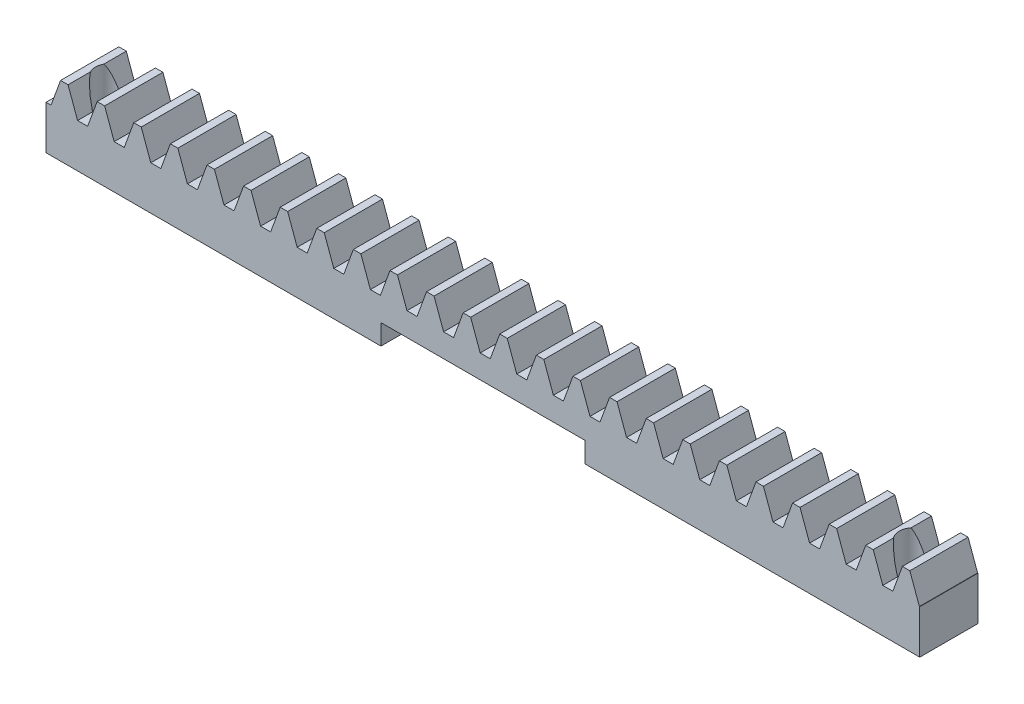
SolidWorks part; units mm, degrees
extrude "Blank" add sketch "BlankSke" against normal blind 10
sketch "BlankSke" plane through (0, 0, 0) normal (0, 0, 1) x (1, 0, 0)
  line L1 (0, 0) -> (150, 0)
  line L2 (0, 0) -> (0, 12)
  line L3 (0, 12) -> (150, 12)
  line L4 (150, 0) -> (150, 12)
  dimension "Length" = 150
  dimension "Blank_height" = 12
ref_plane "Plane1" through (0, 0, 0) normal (0, 0, 1) x (1, 0, 0)
ref_plane "Plane2" through (0, 0, 0) normal (0, 1, 0) x (1, 0, 0)
ref_plane "Plane3" through (0, 0, 0) normal (1, 0, 0) x (0, 0, -1)
other "Configuration Table"
sketch "HoldingSke" plane through (0, 0, 0) normal (0, 1, 0) x (1, 0, 0)
  line L0 (0, 0) -> (0.0696, 0.4951)
  line L1 (-15, 0) -> (100, 0) construction
  line L2 (0, 0) -> (-2.1039, 2.3779)
  line L3 (0, 0) -> (-11.863, 4.5341)
  line L4 (0, 0) -> (7.8269, 3.6497)
  line L5 (0, 0) -> (-23.7986, -8.8762)
  line L6 (0, 0) -> (-10.5278, -7.1032)
  line L9 (-71.009, 38.7566) -> (69.9449, 90.0596)
  line L10 (-76.2, 4.3779) -> (-66.2, 4.3779)
  line L11 (0, 0) -> (-10, 0)
  line L12 (-76.2, 101.6) -> (-76.133, 101.6)
  line L13 (24.9733, 27.94) -> (52.9518, 28.4284)
  line L14 (24.9733, 27.94) -> (24.9743, 27.94)
  line L15 (24.9733, 27.94) -> (100.4006, 29.5858)
  circle A0 centre (0, 0) radius 19.05
  circle A1 centre (0, 0) radius 5
  circle A2 centre (0, 0) radius 12.7
  dimension "MPH" = 10
  dimension "Diameter" = 38.1
  dimension "Num_teeth" = 25
  dimension "Pitch" = 0.5
  dimension "Show_teeth" = 998
  dimension "Thickness" = 12.7
  dimension "Ap" = 20
  dimension "Pitch_height" = 10
  dimension "Width" = 10
  dimension "Backlash" = 0.067
  dimension "Addendum_fac" = 1
  dimension "Dedendum_fac" = 1.25
  dimension "Clearance_fac" = 0.25
  dimension "Dedendum_add" = 0.001
  dimension "Length" = 150
  dimension "Module" = 2
sketch "TooCutSkeIll" plane through (0, 0, 0) normal (0, 0, 1) x (1, 0, 0)
  line L0 (-2.4806, 11.9474) -> (-0.9819, 7.8296)
  line L1 (-0.5111, 7.5) -> (0.5111, 7.5)
  line L2 (0.9819, 7.8296) -> (2.4806, 11.9474)
  line L3 (150, 12) -> (0, 12) construction
  line L4 (0, 0) -> (0, 64.897) construction
  line L5 (-13.208, 10) -> (12.954, 10) construction
  line L6 (0, 0) -> (150, 0) construction
  line L7 (1.7718, 10) -> (1.7718, 48.7463) construction
  line L8 (-1.7718, 10) -> (-1.7718, 48.7463) construction
  line L9 (2.5558, 12) -> (2.5558, 12.0254)
  line L10 (-2.5558, 12) -> (-2.5558, 12.0254)
  line L11 (-2.5558, 12.0254) -> (2.5558, 12.0254)
  arc A0 (0.5111, 7.5) -> (0.9819, 7.8296) centre (0.5111, 8.001) ccw
  arc A1 (-0.9819, 7.8296) -> (-0.5111, 7.5) centre (-0.5111, 8.001) ccw
  arc A2 (2.5558, 12) -> (2.4806, 11.9474) centre (2.5558, 11.92) ccw
  arc A3 (-2.4806, 11.9474) -> (-2.5558, 12) centre (-2.5558, 11.92) ccw
  dimension "Pitch_height" = 10
  dimension "Addendum_plus" = 2.0254
  dimension "Pressure_angle" = 20
  dimension "Gap_width" = 3.5436
  dimension "Dedendum" = 2.5
extrude "ToothCutIll" [suppressed] cut sketch "TooCutSkeIll" against normal through all
sketch "TooCutSkeSim" plane through (0, 0, 0) normal (0, 0, 1) x (1, 0, 0)
  line L0 (0.8619, 7.5) -> (-0.8619, 7.5)
  line L1 (2.509, 12.0254) -> (0.8619, 7.5)
  line L2 (0, 17.4625) -> (0, 53.467) construction
  line L3 (2.509, 12.0254) -> (-2.509, 12.0254)
  line L6 (-2.509, 12.0254) -> (-0.8619, 7.5)
  line L9 (-1.7718, 10) -> (1.7718, 10) construction
  line L10 (0, 0) -> (150, 0) construction
  line L11 (1.7718, 10) -> (1.7718, 53.467) construction
  line L12 (-1.7718, 10) -> (-1.7718, 53.467) construction
  dimension "Pitch_height" = 10
  dimension "Addendum_plus" = 2.0254
  dimension "Pressure_angle" = 20
  dimension "Gap_width" = 3.5436
  dimension "Dedendum" = 2.5
extrude "ToothCutSim" cut sketch "TooCutSkeSim" against normal through all
pattern_linear "TeethCuts" count 25 spacing 6.2832 along (1, 0, 0) of "ToothCutIll", "ToothCutSim"
sketch "Sketch1" plane through (0, 0, 0) normal (0, -1, 0) x (1, 0, 0)
  line L0 (75, 0) -> (75, -10) construction
  line L1 (0, 0) -> (150, 0) construction
  line L2 (0, -10) -> (150, -10) construction
  line L3 (57.5, -10) -> (57.5, 0)
  line L4 (92.5, -10) -> (57.5, -10)
  line L5 (92.5, -10) -> (92.5, 0)
  line L6 (92.5, 0) -> (57.5, 0)
  point P7 (92.5, -5)
  dimension "D1" = 17.5
extrude "Cut-Extrude1" cut sketch "Sketch1" against normal blind 3.5
sketch "Sketch2" plane through (0, 0, 0) normal (0, -1, 0) x (1, 0, 0)
  line L0 (75, 0) -> (75, -10) construction
  line L1 (92.5, 0) -> (57.5, 0) construction
  line L2 (57.5, -10) -> (92.5, -10) construction
  line L3 (0, -5) -> (150, -5) construction
  line L4 (0, -10) -> (0, 0) construction
  line L5 (150, -10) -> (150, 0) construction
  circle A0 centre (6, -5) radius 2.5
  circle A1 centre (144, -5) radius 2.5
  dimension "D1" = 5
  dimension "D2" = 6
extrude "Cut-Extrude2" cut sketch "Sketch2" against normal up to surface (12 mm away) up to face at (141.3717, 12, -5)
equation "' \"Module@HoldingSke\" = 6.35"
equation "' \"Num_teeth@HoldingSke\" = 12"
equation "' \"Ap@HoldingSke\" =  20"
equation "' \"Ap@HoldingSke\" = 20"
equation "' \"Width@HoldingSke\" = 0.25 * 25.4"
equation "' \"Show_teeth@HoldingSke\" = 500"
equation "' \"Backlash@HoldingSke\" = 0.009 * 25.4"
equation "' \"Addendum_fac@HoldingSke\" = 1.0"
equation "' \"Dedendum_fac@HoldingSke\" = 1.25"
equation "' \"Dedendum_add@HoldingSke\" = 0.00005 * 25.4"
equation "' \"Clearance_fac@HoldingSke\" = 0.25"
equation "' \"Pitch_height@HoldingSke\" = 1 * 25.4"
equation "' \"Length@HoldingSke\" = 4.71 * 25.4"
equation "\"Pitch@HoldingSke\" = 1 / \"Module@HoldingSke\""
equation "\"MPH@HoldingSke\" = \"Dedendum_fac@HoldingSke\" / \"Pitch@HoldingSke\" + 2 * \"Dedendum_add@HoldingSke\" + 0.002 * 25.4"
equation "\"MPH@HoldingSke\" = ((sgn( \"MPH@HoldingSke\" - \"Pitch_height@HoldingSke\")+1)*( \"MPH@HoldingSke\" - \"Pitch_height@HoldingSke\"))/2 + \"Pitch_height@HoldingSke\""
equation "\"Blank_height@BlankSke\" = \"Pitch_height@HoldingSke\" + \"Addendum_fac@HoldingSke\"  / \"Pitch@HoldingSke\" "
equation "\"Length@BlankSke\" =  \"Length@HoldingSke\""
equation "\"Face_width@Blank\" = \"Width@HoldingSke\""
equation "\"Pressure_angle@TooCutSkeIll\" = \"Ap@HoldingSke\""
equation "\"Addendum_plus@TooCutSkeIll\" =  \"Addendum_fac@HoldingSke\"  / \"Pitch@HoldingSke\" + 0.001 *25.4"
equation "\"Dedendum@TooCutSkeIll\" = \"Dedendum_fac@HoldingSke\"  / \"Pitch@HoldingSke\""
equation "\"Pitch_height@TooCutSkeIll\" =  \"MPH@HoldingSke\""
equation "\"Gap_width@TooCutSkeIll\" = 3.14159265 / 2 / \"Pitch@HoldingSke\" + 6 * \"Backlash@HoldingSke\""
equation "\"Pressure_angle@TooCutSkeSim\" = \"Ap@HoldingSke\""
equation "\"Addendum_plus@TooCutSkeSim\" =  \"Addendum_fac@HoldingSke\"  / \"Pitch@HoldingSke\" + 0.001 * 25.4"
equation "\"Dedendum@TooCutSkeSim\" = \"Dedendum_fac@HoldingSke\"  / \"Pitch@HoldingSke\""
equation "\"Pitch_height@TooCutSkeSim\" =  \"MPH@HoldingSke\""
equation "\"Gap_width@TooCutSkeSim\" = 3.14159265 / 2 / \"Pitch@HoldingSke\" + 6 * \"Backlash@HoldingSke\""
equation "\"Root_fillet@TooCutSkeIll\" = \"Clearance_fac@HoldingSke\" / \"Pitch@HoldingSke\" + \"Dedendum_add@HoldingSke\""
equation "\"Break_rad@TooCutSkeIll\" = 0.02 / \"Pitch@HoldingSke\" * 2"
equation "\"Linear_pitch@TeethCuts\" = 3.14159265 / \"Pitch@HoldingSke\""
equation "\"Num_teeth@HoldingSke\" = int( ( \"Length@HoldingSke\" + 0 ) / (3.14159265 / \"Pitch@HoldingSke\")) + 0.9999  + 1"
equation " \"Num_teeth@TeethCuts\" = int( \"Show_teeth@HoldingSke\" ) + 1"
equation " \"Num_teeth@TeethCuts\" = ((sgn( \"Num_teeth@TeethCuts\" - \"Num_teeth@HoldingSke\" )-1)*( \"Num_teeth@TeethCuts\" - \"Num_teeth@HoldingSke\" ))/-2+ \"Num_teeth@HoldingSke\""
equation " \"Num_teeth@TeethCuts\" = ((sgn( \"Num_teeth@TeethCuts\" - 2.0)+1)*( \"Num_teeth@TeethCuts\" - 2.0))/2 +2.0"
